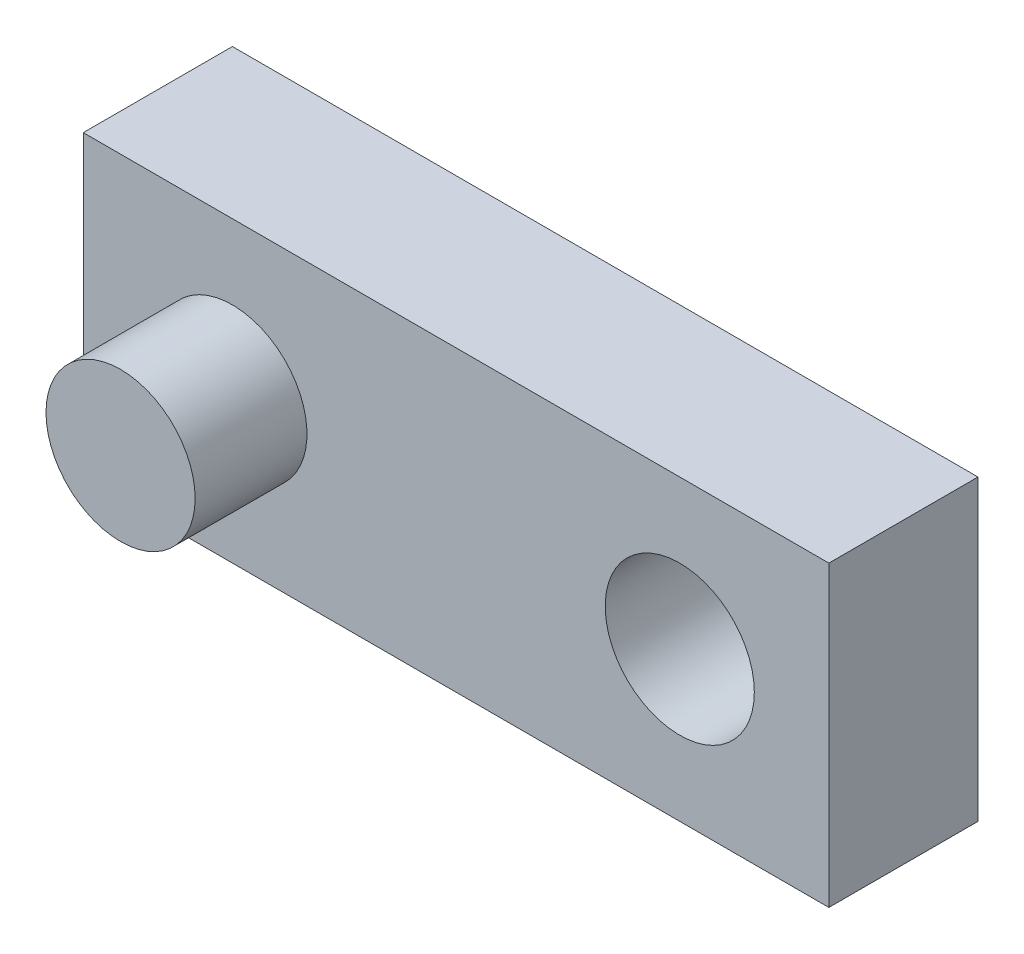
SolidWorks part; units mm, degrees
ref_plane "Front Plane" through (0, 0, 0) normal (0, 0, 1) x (1, 0, 0)
ref_plane "Top Plane" through (0, 0, 0) normal (0, 1, 0) x (1, 0, 0)
ref_plane "Right Plane" through (0, 0, 0) normal (1, 0, 0) x (0, 0, -1)
sketch "Sketch1" plane through (0, 0, 0) normal (0, 0, 1) x (1, 0, 0)
  line L0 (0, 0) -> (50000, 0) construction
  line L1 (0, 0) -> (0, -50000) construction
  line L3 (-1270, -508) -> (1270, -508)
  line L4 (-1270, -508) -> (-1270, 508)
  line L5 (-1270, 508) -> (1270, 508)
  line L6 (1270, -508) -> (1270, 508)
  line L7 (-1270, -508) -> (1270, 508) construction
  line L8 (-1270, 508) -> (1270, -508) construction
  point P5 (0, 0)
  dimension "D1" = 2540
  dimension "D2" = 1016
extrude "Boss-Extrude1" add sketch "Sketch1" along normal blind 508
sketch "Sketch2" plane through (0, 0, 508) normal (0, 0, 1) x (1, 0, 0)
  line L0 (-1270, 508) -> (-1270, -508) construction
  line L1 (1270, -508) -> (1270, 508) construction
  line L2 (1270, 508) -> (-1270, 508) construction
  circle A0 centre (-762, 0) radius 254
  point P6 (1270, 0)
  dimension "D1" = 508
  dimension "D2" = 508
  dimension "D5" = 508
extrude "Boss-Extrude2" add sketch "Sketch2" along normal blind 381
sketch "Sketch3" plane through (0, 0, 508) normal (0, 0, 1) x (1, 0, 0)
  line L0 (1270, -508) -> (1270, 508) construction
  line L1 (-1270, -508) -> (1270, -508) construction
  circle A0 centre (762, 0) radius 254
  dimension "D1" = 508
  dimension "D2" = 508
  dimension "D3" = 508
extrude "Cut-Extrude2" cut sketch "Sketch3" against normal blind 508
